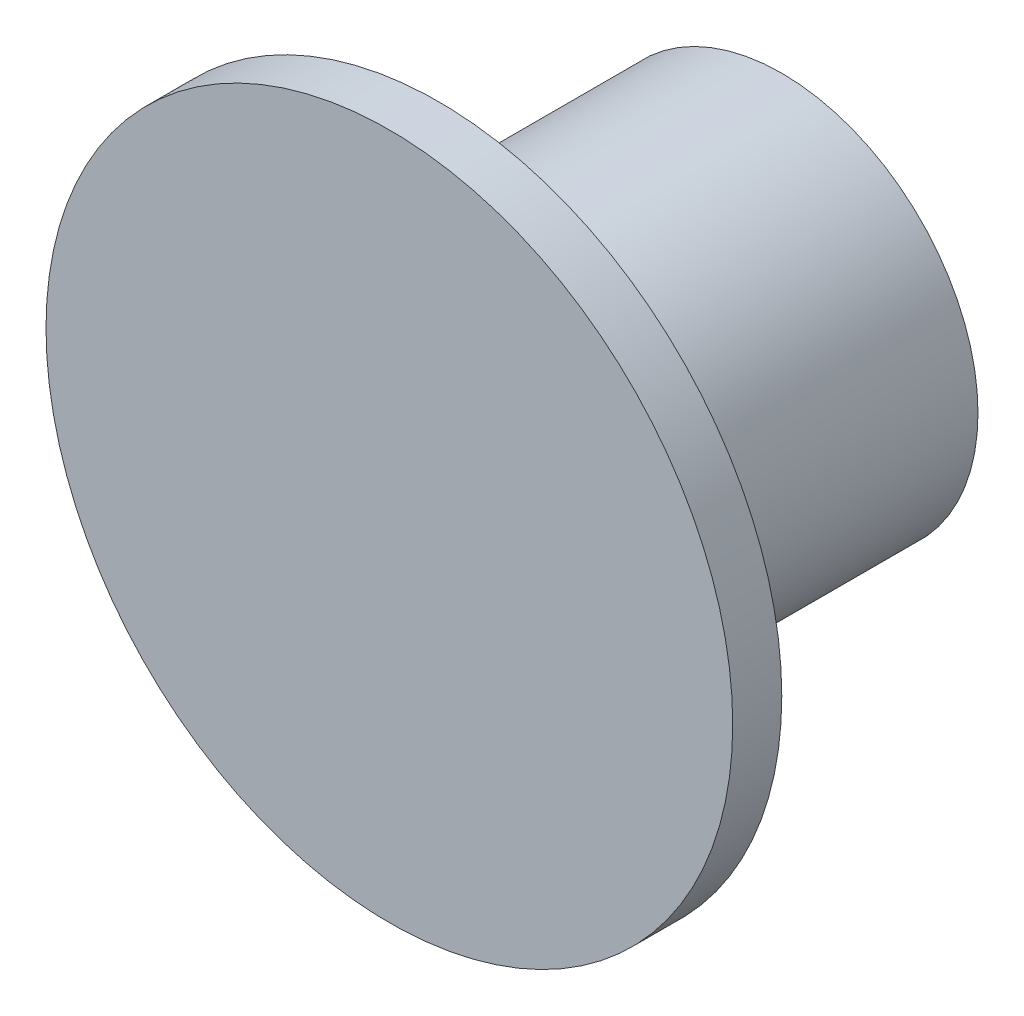
SolidWorks part; units mm, degrees
ref_plane "Front Plane" through (0, 0, 0) normal (0, 0, 1) x (1, 0, 0)
ref_plane "Top Plane" through (0, 0, 0) normal (0, 1, 0) x (1, 0, 0)
ref_plane "Right Plane" through (0, 0, 0) normal (1, 0, 0) x (0, 0, -1)
sketch "Sketch1" plane through (0, 0, 0) normal (0, 0, 1) x (1, 0, 0)
  circle A0 centre (0, 0) radius 4
  dimension "D1" = 8
extrude "Boss-Extrude1" add sketch "Sketch1" along normal blind 7
sketch "Sketch2" plane through (0, 0, 7) normal (0, 0, 1) x (1, 0, 0)
  circle A0 centre (0, 0) radius 7
  dimension "D1" = 14
extrude "Boss-Extrude2" add sketch "Sketch2" along normal blind 1
